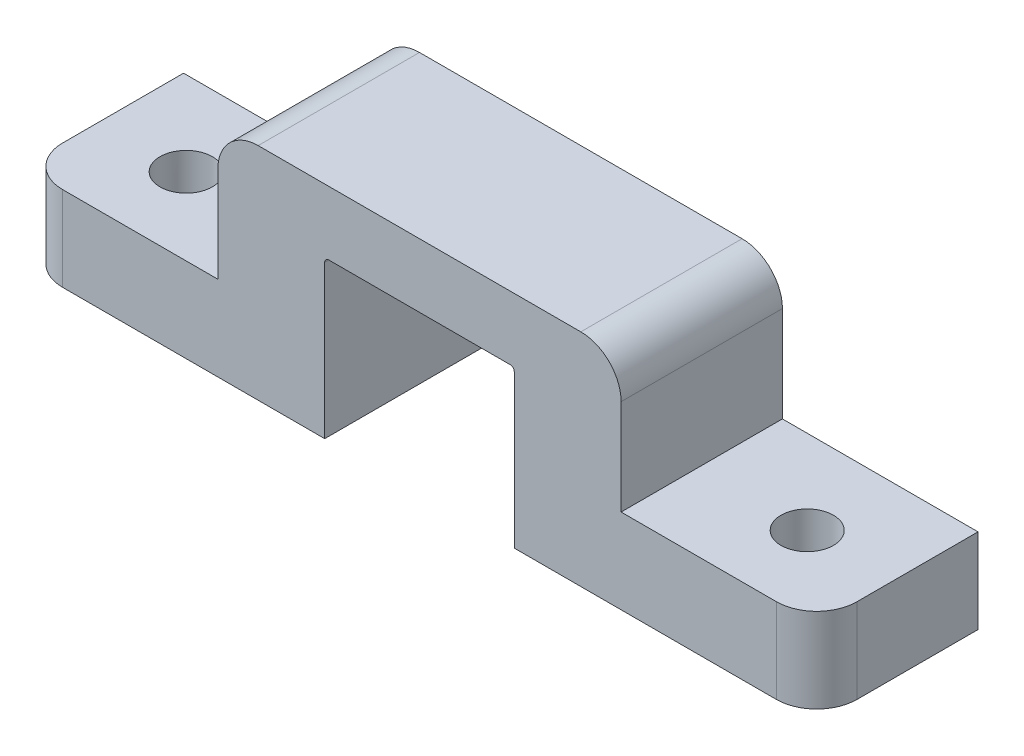
SolidWorks part; units mm, degrees
ref_plane "Front Plane" through (0, 0, 0) normal (0, 0, 1) x (1, 0, 0)
ref_plane "Top Plane" through (0, 0, 0) normal (0, 1, 0) x (1, 0, 0)
ref_plane "Right Plane" through (0, 0, 0) normal (1, 0, 0) x (0, 0, -1)
sketch "Sketch2" plane through (0, 0, 0) normal (0, 0, 1) x (1, 0, 0)
  line L0 (0, -65.1282) -> (0, 70.6641) construction
  line L1 (12.7, 13.894) -> (-12.7, 13.894)
  line L2 (-12.7, 13.894) -> (-12.7, 5.334)
  line L3 (-12.7, 5.334) -> (-25.019, 5.334)
  line L4 (-25.019, 5.334) -> (-25.019, 0)
  line L5 (-25.019, 0) -> (-5.969, 0)
  line L6 (-5.969, 0) -> (-5.969, 9.8778)
  line L7 (-5.969, 9.8778) -> (5.969, 9.8778)
  line L8 (5.969, 0) -> (5.969, 9.8778)
  line L9 (25.019, 0) -> (5.969, 0)
  line L10 (25.019, 5.334) -> (25.019, 0)
  line L11 (12.7, 5.334) -> (25.019, 5.334)
  line L12 (12.7, 13.894) -> (12.7, 5.334)
  point P12 (0, 9.8778)
  point P13 (0, 13.894)
  dimension "D1" = 12.7
  dimension "D2" = 5.969
  dimension "D3" = 19.05
  dimension "D4" = 5.334
extrude "Boss-Extrude1" add sketch "Sketch2" along normal blind 10.16
fillet "Fillet1" radius 2.54 4 edges at (-12.7, 13.894, 5.08) (12.7, 13.894, 5.08) (-25.019, 2.667, 10.16) (25.019, 2.667, 10.16)
sketch "Sketch3" plane through (0, 0, 0) normal (0, 1, 0) x (1, 0, 0)
  line L0 (0, 17.8228) -> (0, -29.1671) construction
  circle A0 centre (-19.558, -5.2962) radius 1.651
  circle A1 centre (19.558, -5.2962) radius 1.651
  dimension "D1" = 19.558
  dimension "D2" = 3.302
extrude "Cut-Extrude1" cut sketch "Sketch3" along normal blind 10.16
fillet "Fillet2" radius 0.254 2 edges at (-5.969, 9.8778, 5.08) (5.969, 9.8778, 5.08)
